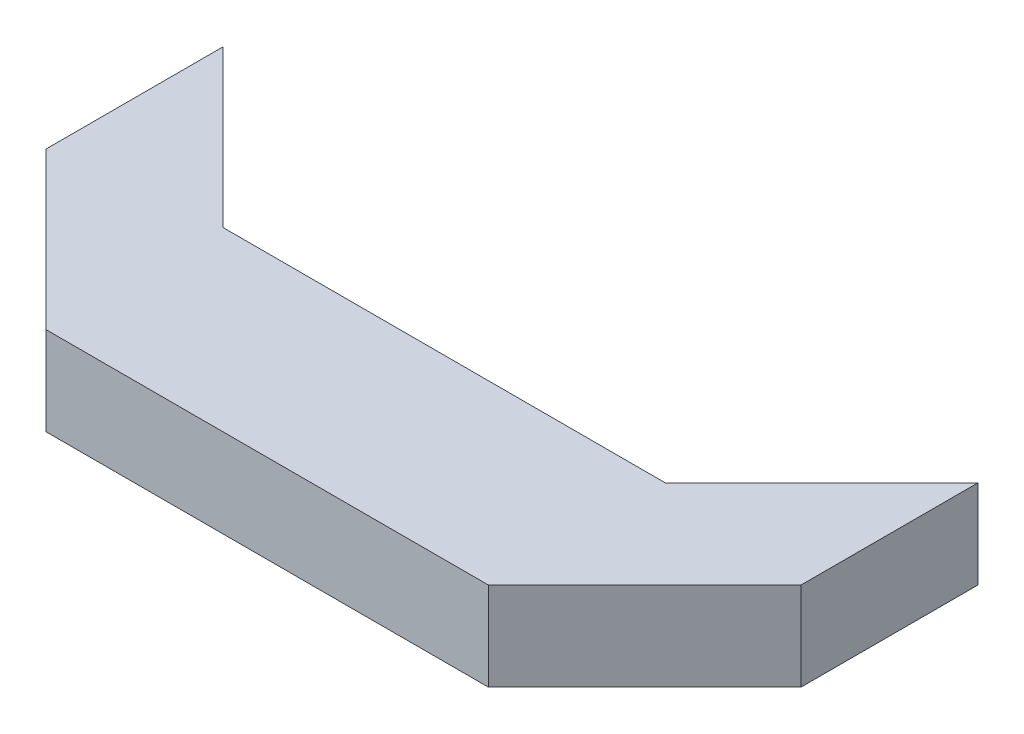
SolidWorks part; units mm, degrees
ref_plane "Front Plane" through (0, 0, 0) normal (0, 0, 1) x (1, 0, 0)
ref_plane "Top Plane" through (0, 0, 0) normal (0, 1, 0) x (1, 0, 0)
ref_plane "Right Plane" through (0, 0, 0) normal (1, 0, 0) x (0, 0, -1)
sketch "Sketch2" plane through (0, 0, 0) normal (0, 1, 0) x (1, 0, 0)
  line L0 (50, 20) -> (85.3553, 55.3553)
  line L1 (-50, 20) -> (50, 20)
  line L3 (-50, -20) -> (50, -20)
  line L5 (-50, 20) -> (50, -20) construction
  line L6 (-50, -20) -> (50, 20) construction
  line L7 (85.3553, 55.3553) -> (85.3553, 15.3553)
  line L8 (85.3553, 15.3553) -> (50, -20)
  line L9 (-50, 20) -> (-85.3553, 55.3553)
  line L10 (-85.3553, 55.3553) -> (-85.3553, 15.3553)
  line L11 (-85.3553, 15.3553) -> (-50, -20)
  point P0 (0, 0)
  dimension "D1" = 100
  dimension "D2" = 40
  dimension "D3" = 50
  dimension "D4" = 135
  dimension "D5" = 135
  dimension "D6" = 135
  dimension "D7" = 135
  dimension "D8" = 50
extrude "Boss-Extrude2" add sketch "Sketch2" along normal blind 20
